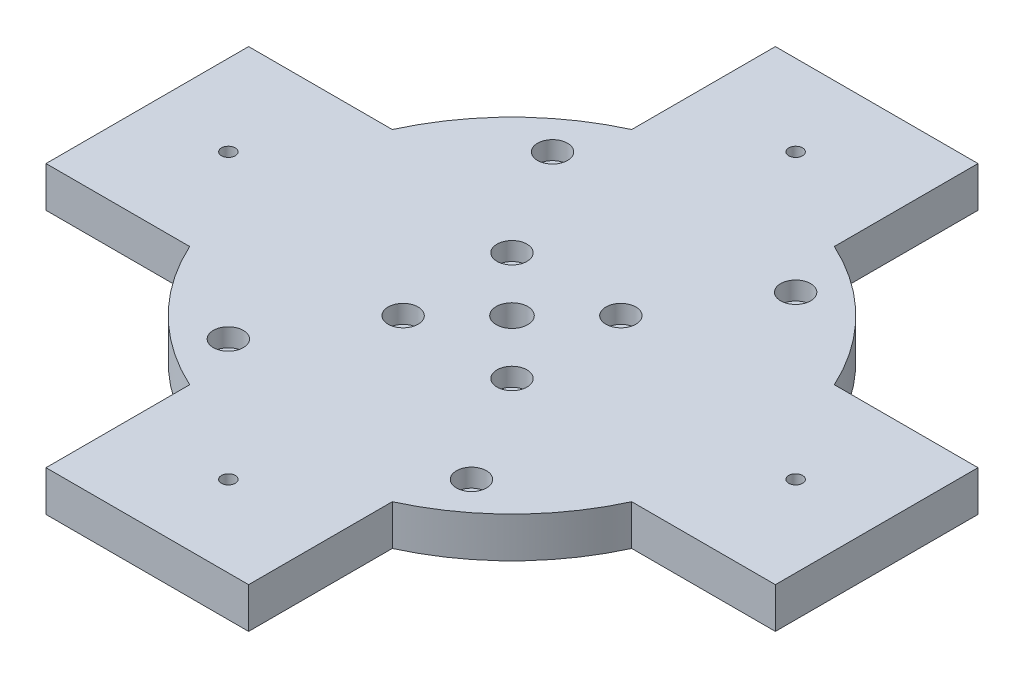
SolidWorks part; units mm, degrees
ref_plane "前视基准面" through (0, 0, 0) normal (0, 0, 1) x (1, 0, 0)
ref_plane "上视基准面" through (0, 0, 0) normal (0, 1, 0) x (1, 0, 0)
ref_plane "右视基准面" through (0, 0, 0) normal (1, 0, 0) x (0, 0, -1)
sketch "草图1" plane through (0, 0, 0) normal (0, 1, 0) x (1, 0, 0)
  circle A0 centre (0, 0) radius 60
  dimension "D1" = 120
extrude "凸台-拉伸1" add sketch "草图1" along normal blind 10
sketch "草图2" plane through (0, 10, 0) normal (0, 1, 0) x (1, 0, 0)
  line L0 (0, 0) -> (0, 27.9787) construction
  line L1 (0, 0) -> (-13.435, 13.435) construction
  circle A0 centre (0, 0) radius 19 construction
  circle A1 centre (-13.435, 13.435) radius 1.7
  circle A2 centre (0, 0) radius 3.9256
  circle A3 centre (13.435, 13.435) radius 1.7
  circle A4 centre (13.435, -13.435) radius 1.7
  circle A5 centre (-13.435, -13.435) radius 1.7
  point P15 (0, 0)
  dimension "D1" = 3.4
  dimension "D2" = 38
  dimension "D4" = 45
  dimension "D3" = 4
extrude "切除-拉伸1" cut sketch "草图2" against normal blind 10
sketch "草图3" plane through (0, 10, 0) normal (0, 1, 0) x (1, 0, 0)
  line L1 (-30, 40) -> (30, 40) construction
  line L2 (-30, 40) -> (-30, -40) construction
  line L3 (-30, -40) -> (30, -40) construction
  line L4 (30, 40) -> (30, -40) construction
  line L5 (-30, 40) -> (30, -40) construction
  line L6 (-30, -40) -> (30, 40) construction
  circle A0 centre (-30, 40) radius 1.7
  circle A1 centre (30, 40) radius 1.7
  circle A2 centre (-30, -40) radius 1.7
  circle A3 centre (30, -40) radius 1.7
  point P0 (0, 0)
  dimension "D3" = 3.4
  dimension "D4" = 3.4
  dimension "D5" = 3.4
  dimension "D6" = 3.4
  dimension "D1" = 80
  dimension "D2" = 60
extrude "切除-拉伸2" cut sketch "草图3" against normal blind 10
sketch "草图4" plane through (0, 10, 0) normal (0, 1, 0) x (1, 0, 0)
  circle A0 centre (-13.435, 13.435) radius 3.7
  circle A1 centre (13.435, 13.435) radius 3.7
  circle A2 centre (13.435, -13.435) radius 3.7
  circle A3 centre (-13.435, -13.435) radius 3.7
  circle A4 centre (-30, 40) radius 3.7
  circle A5 centre (30, 40) radius 3.7
  circle A6 centre (-30, -40) radius 3.7
  circle A7 centre (30, -40) radius 3.7
  point P12 (0, 0)
  point P21 (0, 0)
  dimension "D1" = 7.4
  dimension "D3" = 7.4
  dimension "D4" = 7.4
  dimension "D5" = 7.4
  dimension "D6" = 7.4
  dimension "D2" = 4
extrude "切除-拉伸3" cut sketch "草图4" against normal blind 4.5
sketch "草图5" plane through (0, 10, 0) normal (0, 1, 0) x (1, 0, 0)
  line L0 (25, 25) -> (25, 90)
  line L1 (-25, -90) -> (25, -90)
  line L2 (-25, -90) -> (-25, -25)
  line L3 (-25, 90) -> (25, 90)
  line L4 (25, -90) -> (25, -25)
  line L5 (-25, -90) -> (6.9444, 25) construction
  line L6 (-25, 90) -> (-6.9444, 25) construction
  line L7 (-90, 25) -> (-25, 25)
  line L8 (-90, 25) -> (-90, -25)
  line L9 (-90, -25) -> (-25, -25)
  line L10 (90, 25) -> (90, -25)
  line L11 (-90, 25) -> (90, -25) construction
  line L12 (-90, -25) -> (90, 25) construction
  line L13 (25, 25) -> (90, 25)
  line L14 (0, 0) -> (25, -90) construction
  line L15 (-25, 25) -> (-25, 90)
  line L16 (25, -25) -> (90, -25)
  circle A0 centre (0, 0) radius 3.8932
  circle A1 centre (13.435, 13.435) radius 3.7
  circle A2 centre (-13.435, 13.435) radius 3.7
  circle A3 centre (-13.435, -13.435) radius 3.7
  circle A4 centre (13.435, -13.435) radius 3.7
  point P0 (0, 0)
  point P6 (0, 0)
  dimension "D1" = 50
  dimension "D2" = 180
  dimension "D3" = 50
  dimension "D4" = 180
extrude "凸台-拉伸2" add sketch "草图5" against normal blind 10
sketch "草图6" plane through (0, 0, 0) normal (0, -1, 0) x (1, 0, 0)
  circle A0 centre (0, 0) radius 70 construction
  circle A1 centre (0, -70) radius 1.7
  circle A2 centre (-70, 0) radius 1.7
  circle A3 centre (0, 70) radius 1.7
  circle A4 centre (70, 0) radius 1.7
  point P14 (0, 0)
  dimension "D1" = 140
  dimension "D2" = 3.4
  dimension "D3" = 4
extrude "切除-拉伸4" cut sketch "草图6" against normal blind 10
